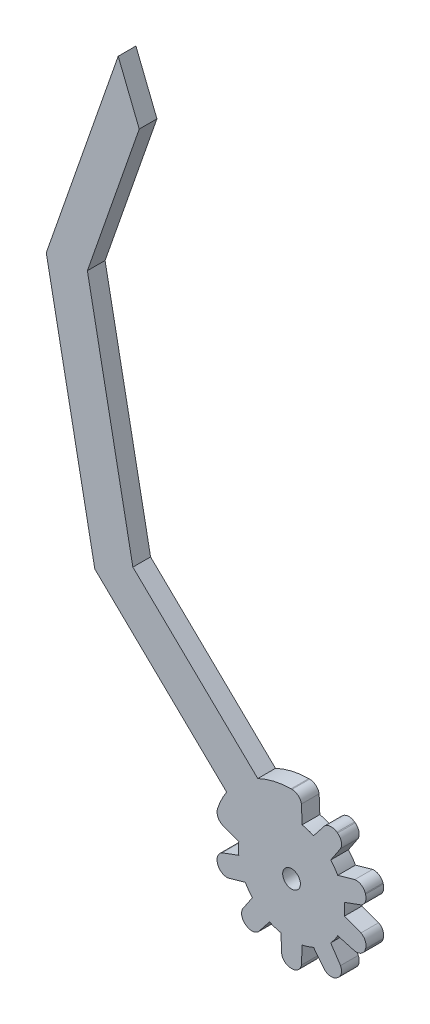
SolidWorks part; units mm, degrees
ref_plane "前基準面" through (0, 0, 0) normal (0, 0, 1) x (1, 0, 0)
ref_plane "上基準面" through (0, 0, 0) normal (0, 1, 0) x (1, 0, 0)
ref_plane "右基準面" through (0, 0, 0) normal (1, 0, 0) x (0, 0, -1)
sketch "草圖1" plane through (0, 0, 0) normal (0, 0, 1) x (1, 0, 0)
  line L0 (0, 15) -> (0, 13.1659) construction
  line L1 (-1.7934, 8.8195) -> (-1.677, 11.8195)
  line L2 (0.0699, 13.1659) -> (-0.0699, 13.1659)
  line L3 (1.7934, 8.8195) -> (1.677, 11.8195)
  line L4 (6.6349, 6.081) -> (8.3041, 8.5764)
  line L5 (7.7953, 10.6103) -> (7.6821, 10.6925)
  line L6 (3.7331, 8.1893) -> (5.5906, 10.5479)
  line L7 (8.942, 1.0198) -> (11.7593, 2.0575)
  line L8 (12.5431, 4.002) -> (12.4999, 4.135)
  line L9 (7.8337, 4.431) -> (10.7228, 5.2474)
  line L10 (7.8337, -4.431) -> (10.7228, -5.2474)
  line L11 (12.4999, -4.135) -> (12.5431, -4.002)
  line L12 (8.942, -1.0198) -> (11.7593, -2.0575)
  line L13 (3.7331, -8.1893) -> (5.5906, -10.5479)
  line L14 (7.6821, -10.6925) -> (7.7953, -10.6103)
  line L15 (6.6349, -6.081) -> (8.3041, -8.5764)
  line L16 (-1.7934, -8.8195) -> (-1.677, -11.8195)
  line L17 (-0.0699, -13.1659) -> (0.0699, -13.1659)
  line L18 (1.7934, -8.8195) -> (1.677, -11.8195)
  line L19 (-6.6349, -6.081) -> (-8.3041, -8.5764)
  line L20 (-7.7953, -10.6103) -> (-7.6821, -10.6925)
  line L21 (-3.7331, -8.1893) -> (-5.5906, -10.5479)
  line L22 (-8.942, -1.0198) -> (-11.7593, -2.0575)
  line L23 (-12.5431, -4.002) -> (-12.4999, -4.135)
  line L24 (-7.8337, -4.431) -> (-10.7228, -5.2474)
  line L25 (-7.8337, 4.431) -> (-10.7228, 5.2474)
  line L26 (-12.4999, 4.135) -> (-12.5431, 4.002)
  line L27 (-8.942, 1.0198) -> (-11.7593, 2.0575)
  line L28 (-3.7331, 8.1893) -> (-5.5906, 10.5479)
  line L29 (-7.6821, 10.6925) -> (-7.7953, 10.6103)
  line L30 (-6.6349, 6.081) -> (-8.3041, 8.5764)
  arc A0 (-1.7934, 8.8195) -> (-3.7331, 8.1893) centre (0, 0) ccw
  arc A1 (-0.0699, 13.1659) -> (-1.677, 11.8195) centre (-0.0699, 11.5335) ccw
  arc A2 (0.0699, 13.1659) -> (1.677, 11.8195) centre (0.0699, 11.5335) cw
  arc A3 (7.7953, 10.6103) -> (8.3041, 8.5764) centre (6.8358, 9.2897) cw
  arc A4 (7.6821, 10.6925) -> (5.5906, 10.5479) centre (6.7226, 9.3719) ccw
  arc A5 (12.5431, 4.002) -> (11.7593, 2.0575) centre (10.9906, 3.4975) cw
  arc A6 (12.4999, 4.135) -> (10.7228, 5.2474) centre (10.9474, 3.6306) ccw
  arc A7 (12.4999, -4.135) -> (10.7228, -5.2474) centre (10.9474, -3.6306) cw
  arc A8 (12.5431, -4.002) -> (11.7593, -2.0575) centre (10.9906, -3.4975) ccw
  arc A9 (7.6821, -10.6925) -> (5.5906, -10.5479) centre (6.7226, -9.3719) cw
  arc A10 (7.7953, -10.6103) -> (8.3041, -8.5764) centre (6.8358, -9.2897) ccw
  arc A11 (-0.0699, -13.1659) -> (-1.677, -11.8195) centre (-0.0699, -11.5335) cw
  arc A12 (0.0699, -13.1659) -> (1.677, -11.8195) centre (0.0699, -11.5335) ccw
  arc A13 (-7.7953, -10.6103) -> (-8.3041, -8.5764) centre (-6.8358, -9.2897) cw
  arc A14 (-7.6821, -10.6925) -> (-5.5906, -10.5479) centre (-6.7226, -9.3719) ccw
  arc A15 (-12.5431, -4.002) -> (-11.7593, -2.0575) centre (-10.9906, -3.4975) cw
  arc A16 (-12.4999, -4.135) -> (-10.7228, -5.2474) centre (-10.9474, -3.6306) ccw
  arc A17 (-12.4999, 4.135) -> (-10.7228, 5.2474) centre (-10.9474, 3.6306) cw
  arc A18 (-12.5431, 4.002) -> (-11.7593, 2.0575) centre (-10.9906, 3.4975) ccw
  arc A19 (-7.6821, 10.6925) -> (-5.5906, 10.5479) centre (-6.7226, 9.3719) cw
  arc A20 (-7.7953, 10.6103) -> (-8.3041, 8.5764) centre (-6.8358, 9.2897) ccw
  arc A21 (3.7331, 8.1893) -> (1.7934, 8.8195) centre (0, 0) ccw
  arc A22 (7.8337, 4.431) -> (6.6349, 6.081) centre (0, 0) ccw
  arc A23 (8.942, -1.0198) -> (8.942, 1.0198) centre (0, 0) ccw
  arc A24 (6.6349, -6.081) -> (7.8337, -4.431) centre (0, 0) ccw
  arc A25 (1.7934, -8.8195) -> (3.7331, -8.1893) centre (0, 0) ccw
  arc A26 (-3.7331, -8.1893) -> (-1.7934, -8.8195) centre (0, 0) ccw
  arc A27 (-7.8337, -4.431) -> (-6.6349, -6.081) centre (0, 0) ccw
  arc A28 (-8.942, 1.0198) -> (-8.942, -1.0198) centre (0, 0) ccw
  arc A29 (-6.6349, 6.081) -> (-7.8337, 4.431) centre (0, 0) ccw
  circle A30 centre (0, 0) radius 1.5
  point P3 (0, 0)
  point P10 (0, 20.7752)
  point P16 (0, 20.7752)
  point P89 (0, 0)
  dimension "D1" = 18
  dimension "D4" = 3
  dimension "D3" = 3
  dimension "D2" = 10
extrude "填料-伸長2" add sketch "草圖1" along normal blind 3
sketch "草圖2" plane through (0, 0, 0) normal (0, 0, 1) x (1, 0, 0)
  line L0 (0.0699, 13.1659) -> (0.0699, 2.18)
  line L1 (0, 0) -> (0.0706, -0.1765)
  line L2 (0.0699, 2.18) -> (-12.4936, 4.1538)
  arc A0 (0.0699, 13.1659) -> (-12.4936, 4.1538) centre (0, 0) ccw
  arc A1 (-10.7228, 5.2474) -> (-12.4999, 4.135) centre (-10.9474, 3.6306) ccw construction
extrude "填料-伸長4" add sketch "草圖2" along normal blind 3 contours A0 L2 L0
sketch "草圖5" plane through (0, 0, 0) normal (0, 0, -1) x (-1, 0, 0)
  line L8 (10.3217, 6.5699) -> (33.3405, 28.799)
  line L9 (5.4591, 11.6053) -> (26.8903, 32.3012)
  line L10 (26.8903, 32.3012) -> (34.5983, 71.9555)
  line L11 (33.3405, 28.799) -> (41.5653, 71.1115)
  line L12 (34.5983, 71.9555) -> (25.8125, 97.136)
  line L13 (41.5653, 71.1115) -> (29.3761, 106.0461)
  line L14 (29.3761, 106.0461) -> (25.8125, 97.136)
  line L15 (5.4591, 11.6053) -> (10.3217, 6.5699)
  line L16 (5.4591, 11.6053) -> (10.3217, 6.5699)
  line L17 (5.4591, 11.6053) -> (10.3217, 6.5699)
  line L18 (8.942, 1.0198) -> (-1.7934, 8.8195) construction
  line L19 (7.8904, 9.0876) -> (3.5743, 4.9196) construction
  dimension "D2" = 32
  dimension "D3" = 145
  dimension "D4" = 43.1045
  dimension "D5" = 40.3966
  dimension "D6" = 6.3
  dimension "D7" = 37
  dimension "D8" = 7
  dimension "D9" = 7
  dimension "D10" = 90
  dimension "D11" = 6
  dimension "D12" = 100
sketch "草圖7" plane through (0, 0, 3) normal (0, 0, 1) x (1, 0, 0)
extrude "填料-伸長6" add sketch "草圖5" against normal blind 3 contours L9 L15 L8 L11 L13 L14 L12 L10
